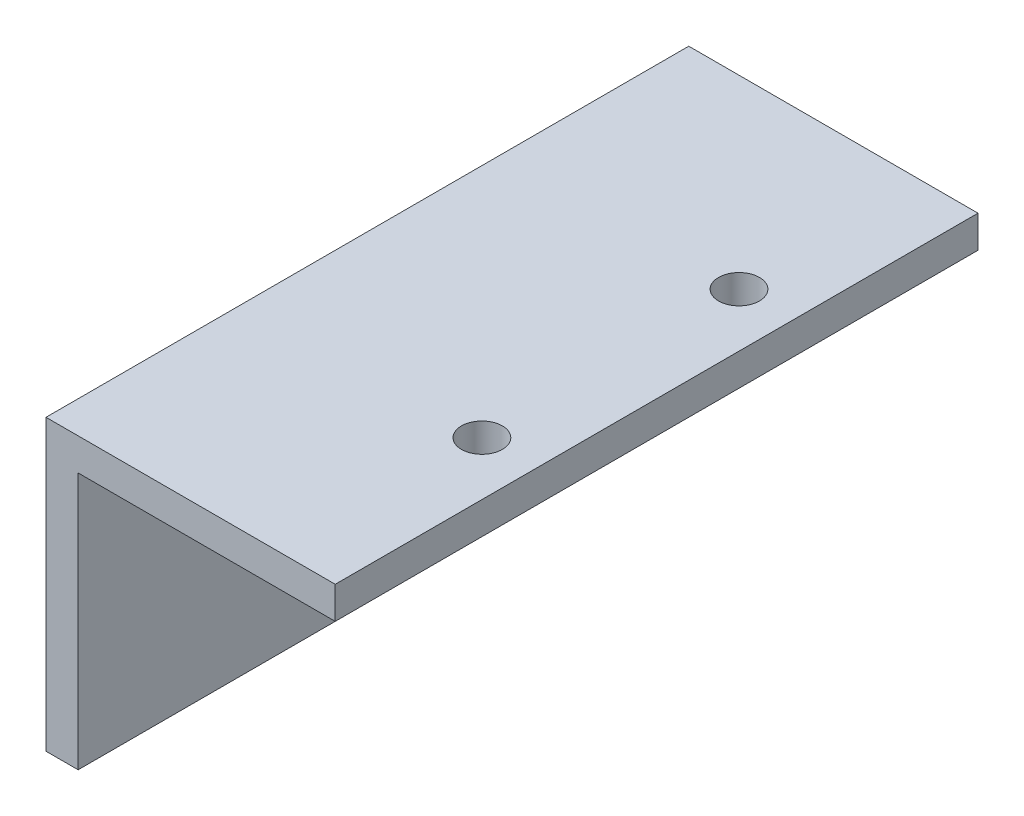
SolidWorks part; units mm, degrees
ref_plane "Front Plane" through (0, 0, 0) normal (0, 0, 1) x (1, 0, 0)
ref_plane "Top Plane" through (0, 0, 0) normal (0, 1, 0) x (1, 0, 0)
ref_plane "Right Plane" through (0, 0, 0) normal (1, 0, 0) x (0, 0, -1)
sketch "Sketch1" plane through (0, 0, 0) normal (0, 0, 1) x (1, 0, 0)
  line L0 (0, 0) -> (0, 28.575)
  line L1 (0, 28.575) -> (28.575, 28.575)
  line L2 (3.175, 0) -> (3.175, 25.4)
  line L3 (3.175, 25.4) -> (28.575, 25.4)
  line L4 (0, 0) -> (3.175, 0)
  line L5 (28.575, 28.575) -> (28.575, 25.4)
  dimension "D1" = 3.175
  dimension "D2" = 28.575
extrude "Boss-Extrude1" add sketch "Sketch1" along normal blind 63.5
sketch "Sketch2" plane through (0, 28.575, 0) normal (0, 1, 0) x (1, 0, 0)
  circle A0 centre (23.275, -43.7102) radius 2.0193 construction
  circle A1 centre (23.275, -43.7102) radius 2.0193
  circle A2 centre (23.275, -18.3102) radius 2.0193 construction
  circle A3 centre (23.275, -18.3102) radius 2.0193
extrude "Cut-Extrude1" cut sketch "Sketch2" against normal up to next
